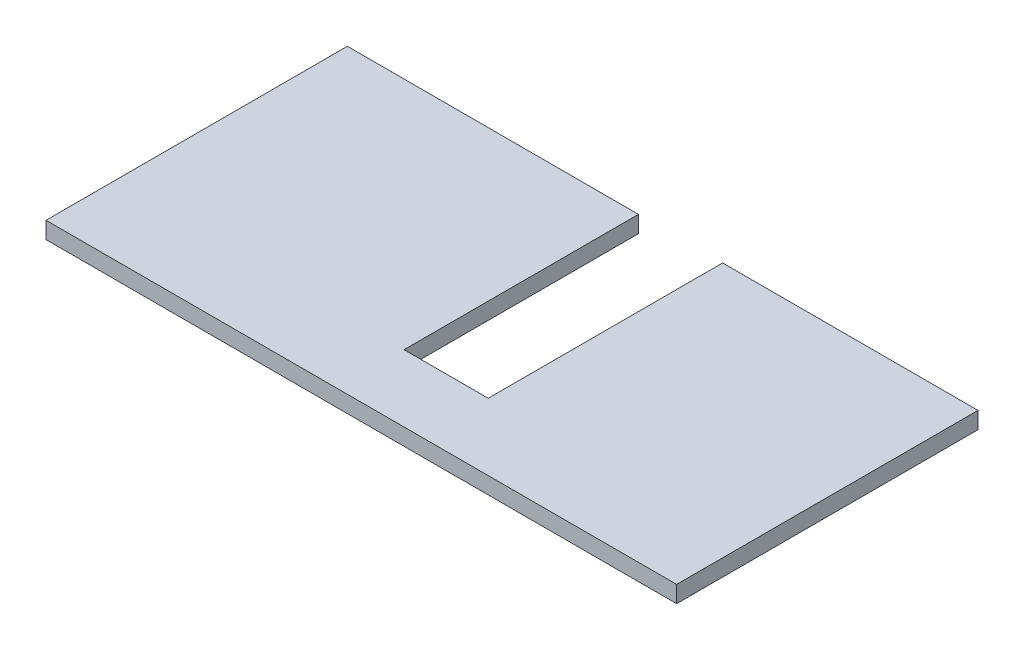
SolidWorks part; units mm, degrees
ref_plane "Plano frontal" through (0, 0, 0) normal (0, 0, 1) x (1, 0, 0)
ref_plane "Plano superior" through (0, 0, 0) normal (0, 1, 0) x (1, 0, 0)
ref_plane "Plano direito" through (0, 0, 0) normal (1, 0, 0) x (0, 0, -1)
sketch "Esboço1" plane through (0, 0, 0) normal (0, 0, 1) x (1, 0, 0)
  line L1 (0, 0) -> (5650, 0)
  line L2 (0, 0) -> (0, 150)
  line L3 (0, 150) -> (5650, 150)
  line L4 (5650, 0) -> (5650, 150)
  dimension "D1" = 150
  dimension "D2" = 5650
extrude "Ressalto-extrusão1" add sketch "Esboço1" along normal blind 2700
sketch "Esboço2" plane through (0, 150, 0) normal (0, 1, 0) x (1, 0, 0)
  line L1 (3362, 0) -> (2608, 0)
  line L2 (3362, 0) -> (3362, -2100)
  line L3 (3362, -2100) -> (2608, -2100)
  line L4 (2608, 0) -> (2608, -2100)
  line L5 (0, -2700) -> (0, 0) construction
  line L6 (5650, 0) -> (0, 0) construction
  dimension "D1" = 754
  dimension "D2" = 2100
  dimension "D3" = 2608
  dimension "D4" = 0
extrude "Corte-extrusão1" cut sketch "Esboço2" against normal through all
